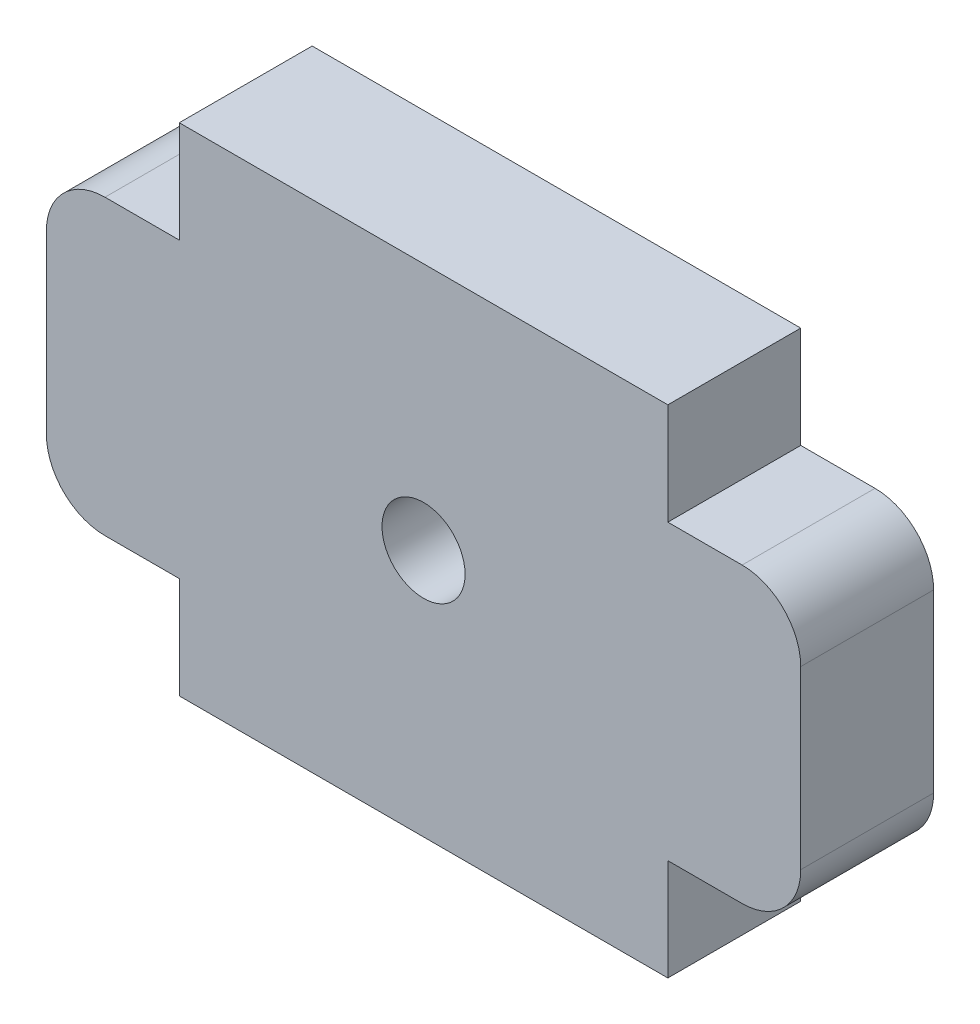
SolidWorks part; units mm, degrees
ref_plane "Front Plane" through (0, 0, 0) normal (0, 0, 1) x (1, 0, 0)
ref_plane "Top Plane" through (0, 0, 0) normal (0, 1, 0) x (1, 0, 0)
ref_plane "Right Plane" through (0, 0, 0) normal (1, 0, 0) x (0, 0, -1)
sketch "Sketch1" plane through (0, 0, 0) normal (0, 0, 1) x (1, 0, 0)
  line L1 (12.5, -12.7) -> (-12.5, -12.7)
  line L2 (12.5, -12.7) -> (12.5, 12.7)
  line L3 (12.5, 12.7) -> (-12.5, 12.7)
  line L4 (-12.5, -12.7) -> (-12.5, 12.7)
  line L5 (12.5, -12.7) -> (-12.5, 12.7) construction
  line L6 (12.5, 12.7) -> (-12.5, -12.7) construction
  point P0 (0, 0)
  dimension "D1" = 25
  dimension "D2" = 25.4
extrude "Boss-Extrude1" add sketch "Sketch1" along normal blind 6.8
sketch "Sketch2" plane through (0, 0, 6.8) normal (0, 0, 1) x (1, 0, 0)
  line L0 (12.5, -12.7) -> (12.5, 12.7) construction
  line L1 (19.3, -7.5) -> (12.5, -7.5)
  line L2 (19.3, -7.5) -> (19.3, 7.5)
  line L3 (19.3, 7.5) -> (12.5, 7.5)
  line L4 (12.5, -7.5) -> (12.5, 7.5)
  line L5 (19.3, -7.5) -> (12.5, 7.5) construction
  line L6 (19.3, 7.5) -> (12.5, -7.5) construction
  point P0 (15.9, 0)
  dimension "D1" = 15
  dimension "D2" = 6.8
extrude "Boss-Extrude2" add sketch "Sketch2" against normal blind 6.8
fillet "Fillet1" radius 3 2 edges at (19.3, 7.5, 3.4) (19.3, -7.5, 3.4)
mirror "Mirror1" about plane through (0, 0, 0) normal (1, 0, 0) of "Boss-Extrude2", "Fillet1"
sketch "Sketch3" plane through (0, 0, 6.8) normal (0, 0, 1) x (1, 0, 0)
  circle A0 centre (0, 0) radius 2.125
  dimension "D1" = 4.25
extrude "Cut-Extrude1" cut sketch "Sketch3" against normal blind 6.8
